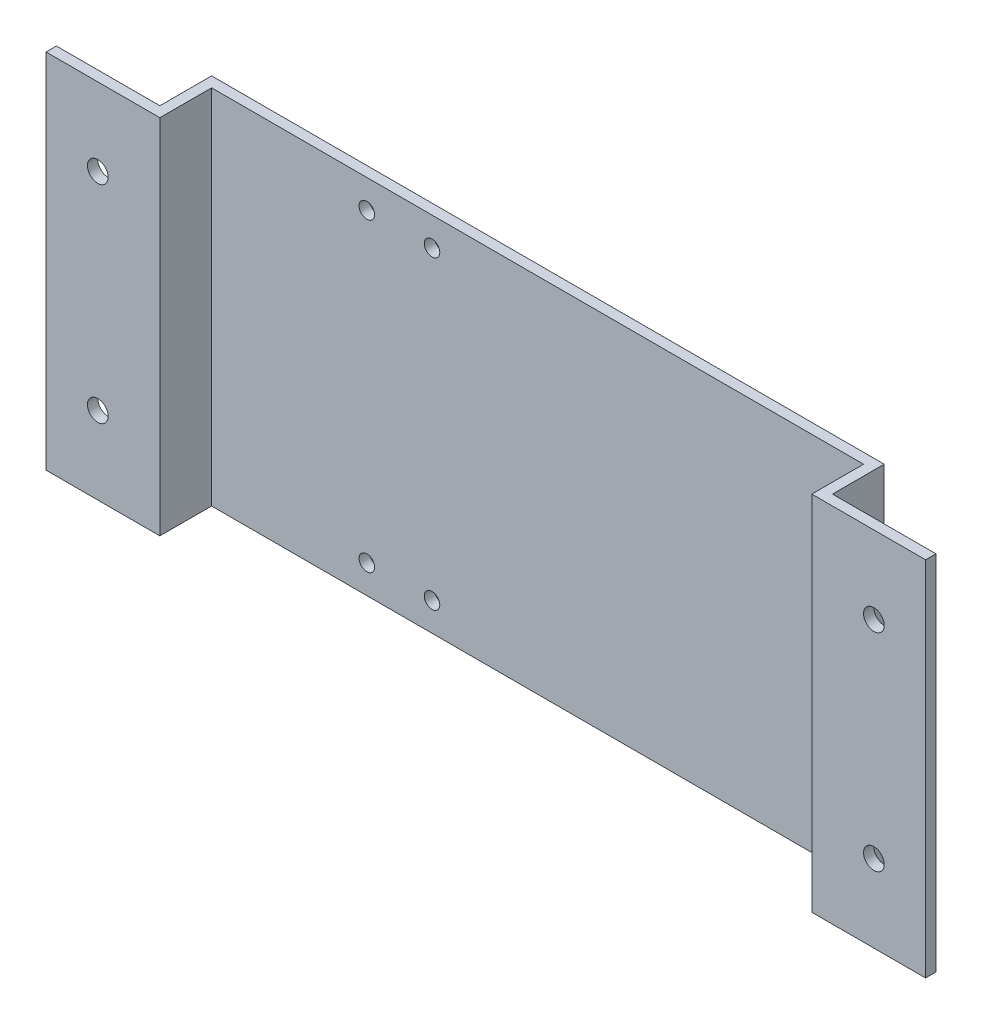
SolidWorks part; units mm, degrees
material "ABS"
ref_plane "Front Plane" through (0, 0, 0) normal (0, 0, 1) x (1, 0, 0)
ref_plane "Top Plane" through (0, 0, 0) normal (0, 1, 0) x (1, 0, 0)
ref_plane "Right Plane" through (0, 0, 0) normal (1, 0, 0) x (0, 0, -1)
sketch "Sketch1" plane through (0, 0, 0) normal (0, 0, 1) x (1, 0, 0)
  line L1 (-63, -35) -> (63, -35)
  line L2 (-63, -35) -> (-63, 35)
  line L3 (-63, 35) -> (63, 35)
  line L4 (63, -35) -> (63, 35)
  line L5 (-63, -35) -> (63, 35) construction
  line L6 (-63, 35) -> (63, -35) construction
  point P0 (0, 0)
  dimension "D1" = 126
  dimension "D2" = 70
extrude "Boss-Extrude1" add sketch "Sketch1" along normal blind 2
sketch "Sketch2" plane through (0, 0, 2) normal (0, 0, 1) x (1, 0, 0)
  line L0 (0, 53.0637) -> (0, -53.0637) construction
  line L1 (-92.4545, 0) -> (92.4545, 0) construction
  line L3 (-33, -29.5) -> (-20.4, -29.5) construction
  line L4 (-33, -29.5) -> (-33, 29.5) construction
  line L5 (-33, 29.5) -> (-20.4, 29.5) construction
  line L6 (-20.4, -29.5) -> (-20.4, 29.5) construction
  line L7 (-33, -29.5) -> (-20.4, 29.5) construction
  line L8 (-33, 29.5) -> (-20.4, -29.5) construction
  circle A2 centre (-20.4, 29.5) radius 1.5
  circle A3 centre (-33, 29.5) radius 1.5
  circle A6 centre (-20.4, -29.5) radius 1.5
  circle A7 centre (-33, -29.5) radius 1.5
  point P5 (0, 0)
  point P6 (0, 0)
  point P7 (-26.7, 0)
  dimension "D6" = 3
  dimension "D7" = 3
  dimension "D12" = 3
  dimension "D13" = 3
  dimension "D1" = 59
  dimension "D2" = 12.6
  dimension "D3" = 20.4
extrude "Cut-Extrude1" cut sketch "Sketch2" against normal up to next
sketch "Sketch3" plane through (0, 35, 0) normal (0, 1, 0) x (1, 0, 0)
  line L0 (-63, 0) -> (-63, -12)
  line L1 (-63, -12) -> (-85, -12)
  line L2 (-85, -12) -> (-85, -10)
  line L3 (-85, -10) -> (-65, -10)
  line L4 (-65, -10) -> (-65, 0)
  line L5 (-65, 0) -> (-63, 0)
  line L6 (63, -2) -> (-63, -2) construction
  dimension "D1" = 2
  dimension "D2" = 2
  dimension "D3" = 10
  dimension "D4" = 20
extrude "Boss-Extrude2" add sketch "Sketch3" against normal up to surface (70 mm away) up to face at (0, -35, 1)
mirror "Mirror1" about plane through (0, 0, 0) normal (1, 0, 0) of "Boss-Extrude2"
sketch "Sketch4" plane through (0, 0, 10) normal (0, 0, -1) x (-1, 0, 0)
  line L0 (-75, 47.3488) -> (-75, -47.772) construction
  line L1 (75, 47.3488) -> (75, -47.772) construction
  line L2 (-108.4802, 20) -> (114.1013, 20) construction
  line L3 (-108.4802, -20) -> (111.7282, -20) construction
  line L4 (-85, -35) -> (-85, 35) construction
  line L5 (85, -35) -> (85, 35) construction
  circle A0 centre (-75, 20) radius 2
  circle A1 centre (-75, -20) radius 2
  circle A2 centre (75, 20) radius 2
  circle A3 centre (75, -20) radius 2
  dimension "D5" = 4
  dimension "D6" = 4
  dimension "D7" = 4
  dimension "D8" = 4
  dimension "D1" = 20
  dimension "D2" = 20
  dimension "D3" = 10
  dimension "D4" = 10
extrude "Cut-Extrude2" cut sketch "Sketch4" against normal up to next
